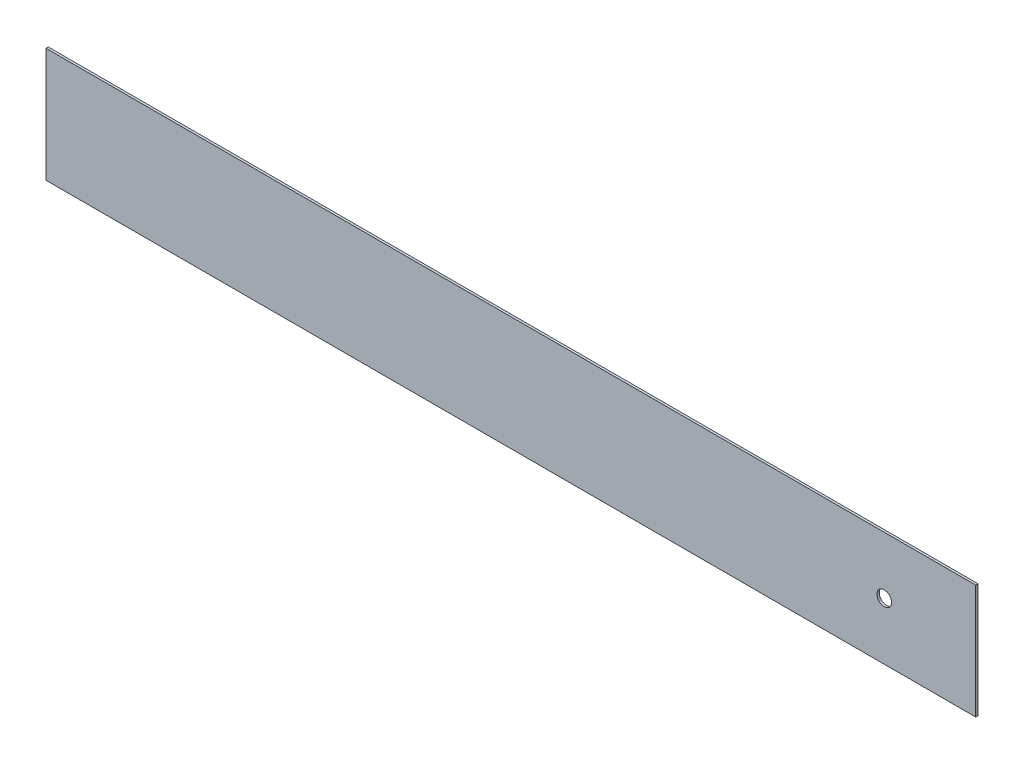
SolidWorks part; units mm, degrees
ref_plane "Front Plane" through (0, 0, 0) normal (0, 0, 1) x (1, 0, 0)
ref_plane "Top Plane" through (0, 0, 0) normal (0, 1, 0) x (1, 0, 0)
ref_plane "Right Plane" through (0, 0, 0) normal (1, 0, 0) x (0, 0, -1)
sketch "Sketch1" plane through (0, 0, 0) normal (0, 0, 1) x (1, 0, 0)
  line L1 (-610, 75) -> (610, 75)
  line L2 (-610, 75) -> (-610, -75)
  line L3 (-610, -75) -> (610, -75)
  line L4 (610, 75) -> (610, -75)
  line L5 (-610, 75) -> (610, -75) construction
  line L6 (-610, -75) -> (610, 75) construction
  circle A0 centre (490, 0) radius 9.6
  point P0 (0, 0)
  dimension "D3" = 75
  dimension "D4" = 120
  dimension "D5" = 19.2
  dimension "D1" = 150
  dimension "D2" = 1220
extrude "Boss-Extrude1" add sketch "Sketch1" along normal blind 3
